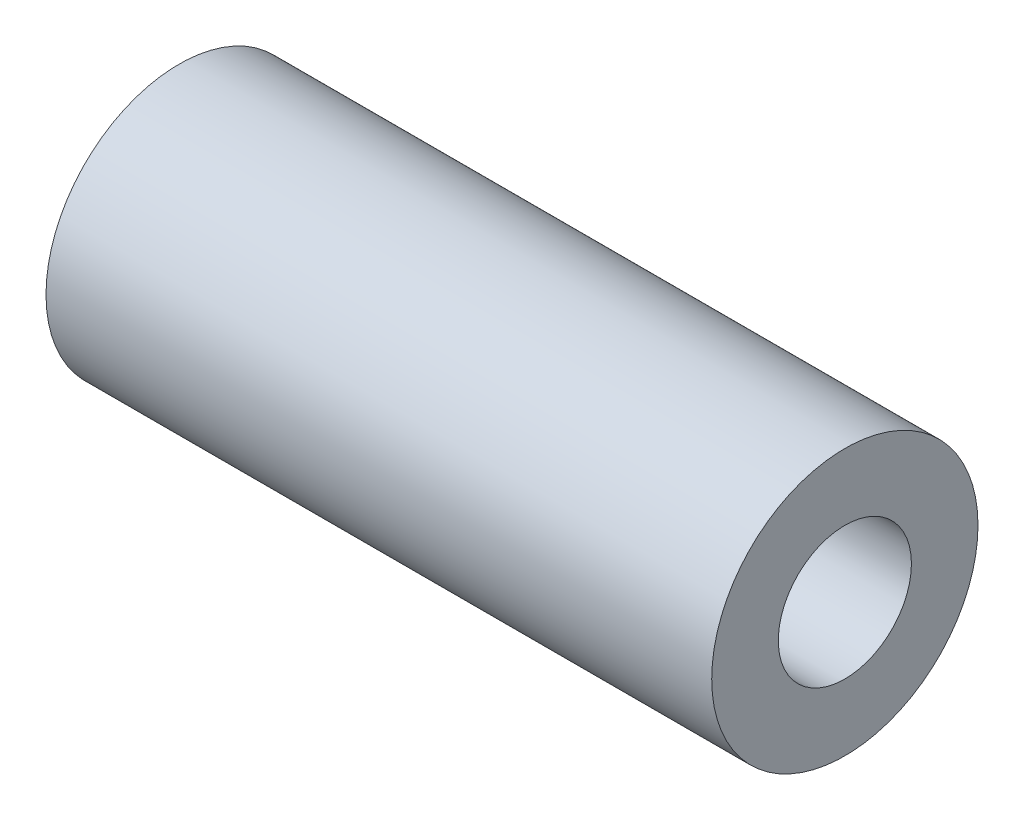
SolidWorks part; units mm, degrees
material "POLYURETHANE (11671)"
ref_plane "Front Plane" through (0, 0, 0) normal (0, 0, 1) x (1, 0, 0)
ref_plane "Top Plane" through (0, 0, 0) normal (0, 1, 0) x (1, 0, 0)
ref_plane "Right Plane" through (0, 0, 0) normal (1, 0, 0) x (0, 0, -1)
sketch "Sketch1" plane through (0, 0, 0) normal (1, 0, 0) x (0, 0, -1)
  circle A0 centre (0, 0) radius 12.7
  circle A1 centre (0, 0) radius 25.4
  dimension "D1" = 25.4
  dimension "D2" = 50.8
extrude "Boss-Extrude1" add sketch "Sketch1" along normal mid plane 127
